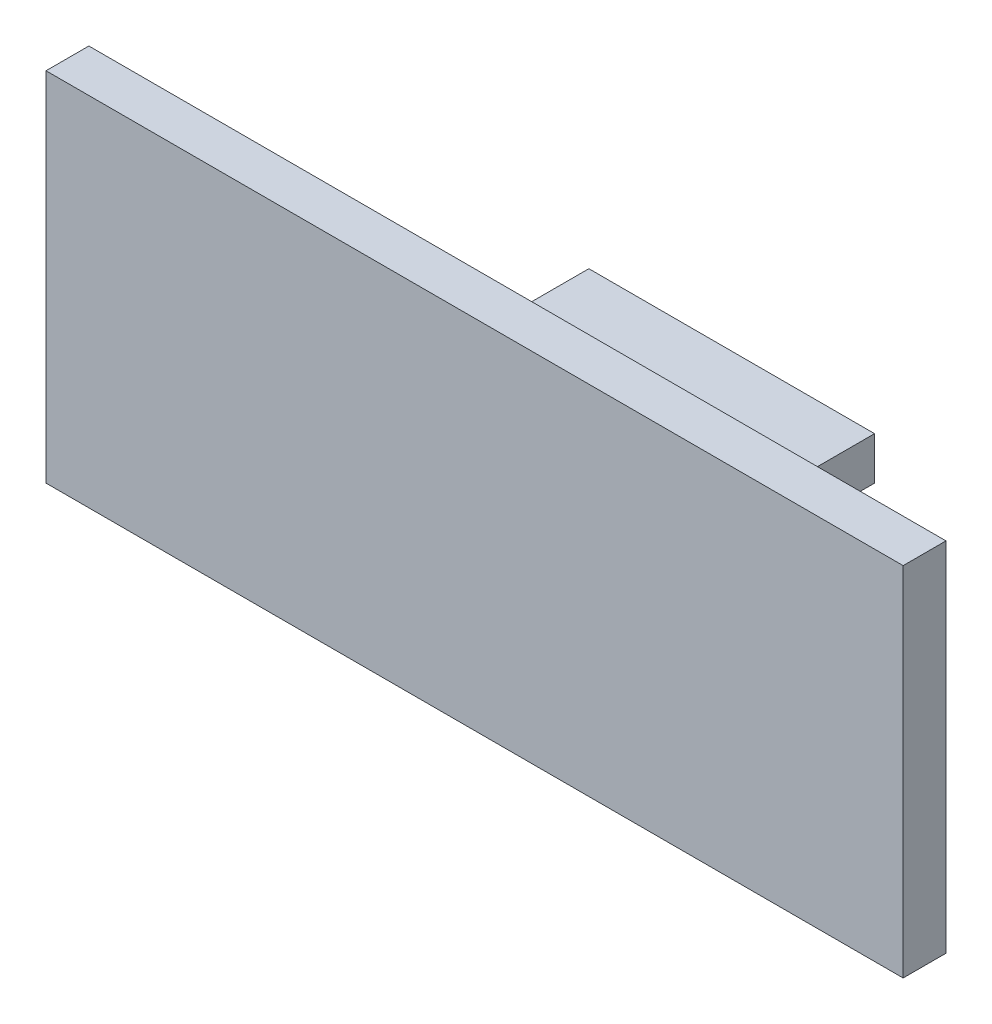
SolidWorks part; units mm, degrees
ref_plane "Alzado" through (0, 0, 0) normal (0, 0, 1) x (1, 0, 0)
ref_plane "Planta" through (0, 0, 0) normal (0, 1, 0) x (1, 0, 0)
ref_plane "Vista lateral" through (0, 0, 0) normal (1, 0, 0) x (0, 0, -1)
sketch "Croquis1" plane through (0, 0, 0) normal (0, 0, 1) x (1, 0, 0)
  line L1 (-30, 12.5) -> (30, 12.5)
  line L2 (-30, 12.5) -> (-30, -12.5)
  line L3 (-30, -12.5) -> (30, -12.5)
  line L4 (30, 12.5) -> (30, -12.5)
  line L5 (-30, 12.5) -> (30, -12.5) construction
  line L6 (-30, -12.5) -> (30, 12.5) construction
  point P0 (0, 0)
  dimension "D1" = 60
  dimension "D2" = 25
extrude "Saliente-Extruir1" add sketch "Croquis1" along normal blind 5
sketch "Croquis2" plane through (0, 0, 0) normal (0, 0, -1) x (-1, 0, 0)
  line L1 (-10, 1.5) -> (10, 1.5)
  line L2 (-10, 1.5) -> (-10, -1.5)
  line L3 (-10, -1.5) -> (10, -1.5)
  line L4 (10, 1.5) -> (10, -1.5)
  line L5 (-10, 1.5) -> (10, -1.5) construction
  line L6 (-10, -1.5) -> (10, 1.5) construction
  point P0 (0, 0)
  dimension "D1" = 20
  dimension "D2" = 3
extrude "Saliente-Extruir2" add sketch "Croquis2" along normal blind 10
sketch "Croquis3" plane through (0, 0, 5) normal (0, 0, 1) x (1, 0, 0)
  line L1 (30, -12.5) -> (-30, -12.5)
  line L2 (30, -12.5) -> (30, 12.5)
  line L3 (30, 12.5) -> (-30, 12.5)
  line L4 (-30, -12.5) -> (-30, 12.5)
  line L5 (30, -12.5) -> (-30, 12.5) construction
  line L6 (30, 12.5) -> (-30, -12.5) construction
  point P0 (0, 0)
extrude "Cortar-Extruir1" cut sketch "Croquis3" against normal blind 2
sketch "Croquis4" plane through (0, 0, -10) normal (0, 0, -1) x (-1, 0, 0)
  line L1 (-10, 1.5) -> (10, 1.5)
  line L2 (-10, 1.5) -> (-10, -1.5)
  line L3 (-10, -1.5) -> (10, -1.5)
  line L4 (10, 1.5) -> (10, -1.5)
extrude "Saliente-Extruir3" add sketch "Croquis4" along normal blind 5
